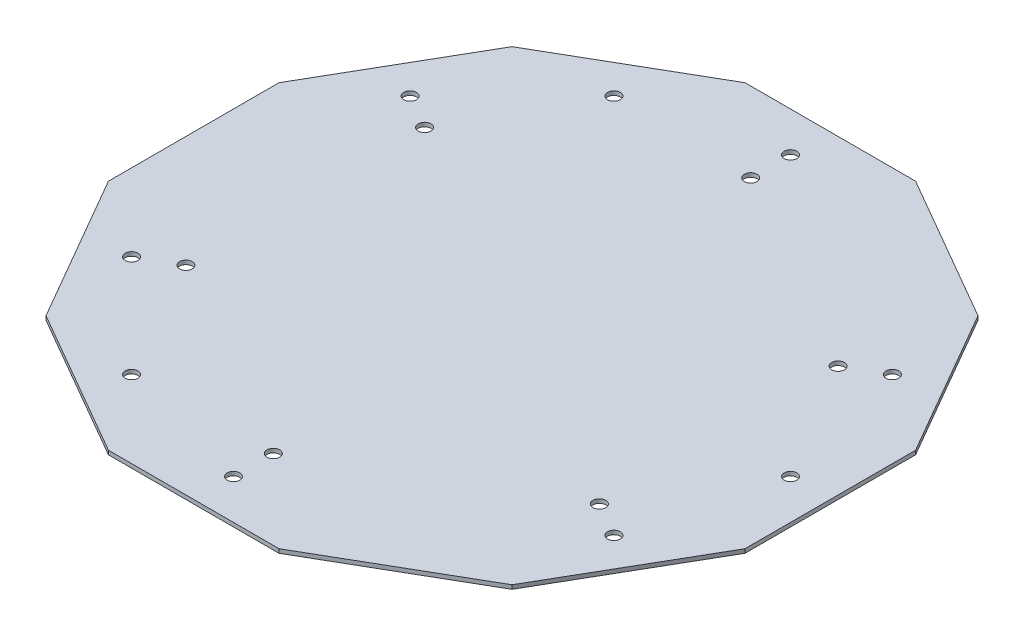
SolidWorks part; units mm, degrees
ref_plane "正面" through (0, 0, 0) normal (0, 0, 1) x (1, 0, 0)
ref_plane "平面" through (0, 0, 0) normal (0, 1, 0) x (1, 0, 0)
ref_plane "右側面" through (0, 0, 0) normal (1, 0, 0) x (0, 0, -1)
other "重心"
sketch "ｽｹｯﾁ8" plane through (0, 0, 0) normal (0, 1, 0) x (1, 0, 0)
  line L0 (-80, -21.4359) -> (-58.5641, -58.5641)
  line L1 (80, 21.4359) -> (58.5641, 58.5641)
  line L2 (58.5641, 58.5641) -> (21.4359, 80)
  line L3 (21.4359, 80) -> (-21.4359, 80)
  line L4 (-21.4359, 80) -> (-58.5641, 58.5641)
  line L5 (-58.5641, 58.5641) -> (-80, 21.4359)
  line L6 (-80, 21.4359) -> (-80, -21.4359)
  line L7 (-58.5641, -58.5641) -> (-21.4359, -80)
  line L8 (-21.4359, -80) -> (21.4359, -80)
  line L9 (21.4359, -80) -> (58.5641, -58.5641)
  line L10 (58.5641, -58.5641) -> (80, -21.4359)
  line L11 (80, -21.4359) -> (80, 21.4359)
  circle A0 centre (0, 0) radius 80 construction
extrude "ﾎﾞｽ - 押し出し2" add sketch "ｽｹｯﾁ8" along normal blind 1
sketch "ｽｹｯﾁ9" plane through (0, 1, 0) normal (0, 1, 0) x (1, 0, 0)
  circle A0 centre (-60.6218, 35) radius 1.6
extrude "ｶｯﾄ - 押し出し5" cut sketch "ｽｹｯﾁ9" against normal blind 1
sketch "ｽｹｯﾁ10" plane through (0, 1, 0) normal (0, 1, 0) x (1, 0, 0)
  circle A0 centre (-51.9615, 30) radius 1.6
extrude "ｶｯﾄ - 押し出し6" cut sketch "ｽｹｯﾁ10" against normal blind 1
sketch "ｽｹｯﾁ11" plane through (0, 1, 0) normal (0, 1, 0) x (1, 0, 0)
  circle A0 centre (60.6218, -35) radius 1.6
extrude "ｶｯﾄ - 押し出し7" cut sketch "ｽｹｯﾁ11" against normal blind 1
sketch "ｽｹｯﾁ12" plane through (0, 1, 0) normal (0, 1, 0) x (1, 0, 0)
  circle A0 centre (51.9615, -30) radius 1.6
extrude "ｶｯﾄ - 押し出し8" cut sketch "ｽｹｯﾁ12" against normal blind 1
sketch "ｽｹｯﾁ16" plane through (0, 1, 0) normal (0, 1, 0) x (1, 0, 0)
  circle A0 centre (60.6218, 35) radius 1.6
extrude "ｶｯﾄ - 押し出し9" cut sketch "ｽｹｯﾁ16" against normal blind 1
sketch "ｽｹｯﾁ17" plane through (0, 1, 0) normal (0, 1, 0) x (1, 0, 0)
  circle A0 centre (51.9615, 30) radius 1.6
extrude "ｶｯﾄ - 押し出し10" cut sketch "ｽｹｯﾁ17" against normal blind 1
sketch "ｽｹｯﾁ18" plane through (0, 1, 0) normal (0, 1, 0) x (1, 0, 0)
  circle A0 centre (-60.6218, -35) radius 1.6
extrude "ｶｯﾄ - 押し出し11" cut sketch "ｽｹｯﾁ18" against normal blind 1
sketch "ｽｹｯﾁ19" plane through (0, 1, 0) normal (0, 1, 0) x (1, 0, 0)
  circle A0 centre (-51.9615, -30) radius 1.6
extrude "ｶｯﾄ - 押し出し12" cut sketch "ｽｹｯﾁ19" against normal blind 1
sketch "ｽｹｯﾁ20" plane through (0, 1, 0) normal (0, 1, 0) x (1, 0, 0)
  circle A0 centre (0, 70) radius 1.6
extrude "ｶｯﾄ - 押し出し13" cut sketch "ｽｹｯﾁ20" against normal blind 1
sketch "ｽｹｯﾁ21" plane through (0, 1, 0) normal (0, 1, 0) x (1, 0, 0)
  circle A0 centre (0, 60) radius 1.6
extrude "ｶｯﾄ - 押し出し14" cut sketch "ｽｹｯﾁ21" against normal blind 1
sketch "ｽｹｯﾁ22" plane through (0, 1, 0) normal (0, 1, 0) x (1, 0, 0)
  circle A0 centre (0, -70) radius 1.6
extrude "ｶｯﾄ - 押し出し15" cut sketch "ｽｹｯﾁ22" against normal blind 1
sketch "ｽｹｯﾁ23" plane through (0, 1, 0) normal (0, 1, 0) x (1, 0, 0)
  circle A0 centre (0, -60) radius 1.6
extrude "ｶｯﾄ - 押し出し16" cut sketch "ｽｹｯﾁ23" against normal blind 1
sketch "ｽｹｯﾁ24" plane through (0, 1, 0) normal (0, 1, 0) x (1, 0, 0)
  circle A0 centre (-35, 60.6218) radius 1.6
extrude "ｶｯﾄ - 押し出し17" cut sketch "ｽｹｯﾁ24" against normal up to next
sketch "ｽｹｯﾁ25" plane through (0, 1, 0) normal (0, 1, 0) x (1, 0, 0)
  circle A0 centre (-35, -60.6218) radius 1.6
extrude "ｶｯﾄ - 押し出し18" cut sketch "ｽｹｯﾁ25" against normal up to next
sketch "ｽｹｯﾁ26" plane through (0, 1, 0) normal (0, 1, 0) x (1, 0, 0)
  circle A0 centre (70, 0) radius 1.6
extrude "ｶｯﾄ - 押し出し19" cut sketch "ｽｹｯﾁ26" against normal up to next
